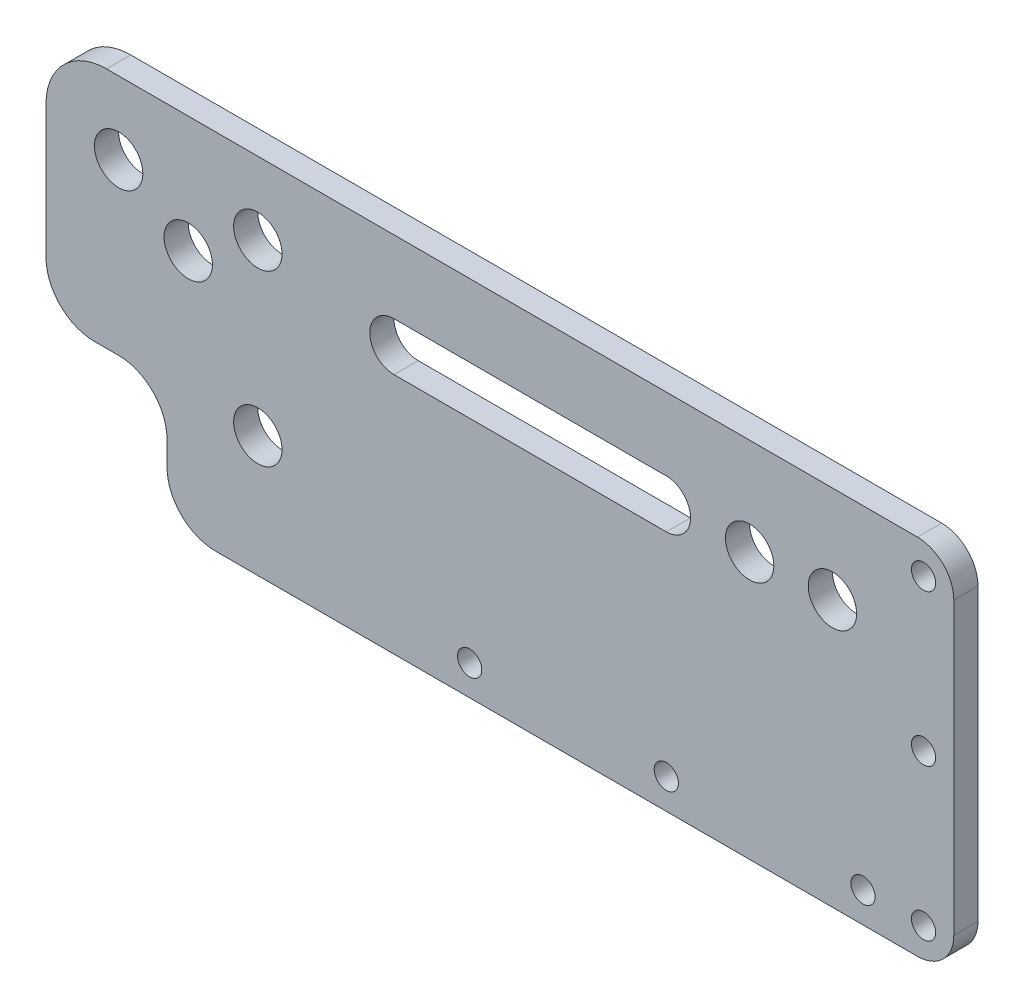
SolidWorks part; units mm, degrees
ref_plane "Front Plane" through (0, 0, 0) normal (0, 0, 1) x (1, 0, 0)
ref_plane "Top Plane" through (0, 0, 0) normal (0, 1, 0) x (1, 0, 0)
ref_plane "Right Plane" through (0, 0, 0) normal (1, 0, 0) x (0, 0, -1)
sketch "Sketch1" plane through (0, 0, 0) normal (0, 0, 1) x (1, 0, 0)
  line L0 (57.5, 44) -> (102.5, 44) construction
  line L1 (28, 0) -> (140, 0)
  line L2 (0, 28) -> (0, 50)
  line L3 (10, 60) -> (140, 60)
  line L5 (57.5, 48) -> (102.5, 48)
  line L6 (57.5, 40) -> (102.5, 40)
  line L7 (8, 20) -> (12, 20)
  line L8 (20, 12) -> (20, 8)
  line L12 (140, 0) -> (144, 0)
  line L13 (140, 60) -> (144, 60)
  line L14 (150, 54) -> (150, 6)
  arc A3 (0, 50) -> (10, 60) centre (10, 50) cw
  circle A4 centre (35, 20) radius 4
  arc A5 (57.5, 48) -> (57.5, 40) centre (57.5, 44) ccw
  arc A6 (102.5, 40) -> (102.5, 48) centre (102.5, 44) ccw
  circle A7 centre (116.2648, 44) radius 4
  circle A8 centre (129.9477, 44) radius 4
  arc A9 (20, 8) -> (28, 0) centre (28, 8) ccw
  arc A10 (12, 20) -> (20, 12) centre (12, 12) cw
  arc A11 (8, 20) -> (0, 28) centre (8, 28) cw
  circle A12 centre (12, 48) radius 4
  circle A13 centre (23.5, 40.7199) radius 4
  circle A14 centre (35, 48) radius 4
  circle A18 centre (135, 5) radius 2
  circle A19 centre (102.5, 5) radius 2
  circle A20 centre (70, 5) radius 2
  circle A21 centre (145, 54.8986) radius 2
  circle A22 centre (145, 29.8986) radius 2
  circle A23 centre (145, 4.8986) radius 2
  arc A24 (144, 0) -> (150, 6) centre (144, 6) ccw
  arc A25 (144, 60) -> (150, 54) centre (144, 54) cw
  point P7 (0, 0)
  point P16 (80, 44)
  dimension "D1" = 8
  dimension "D2" = 3
  dimension "D3" = 6
extrude "Boss-Extrude1" add sketch "Sketch1" along normal blind 4
